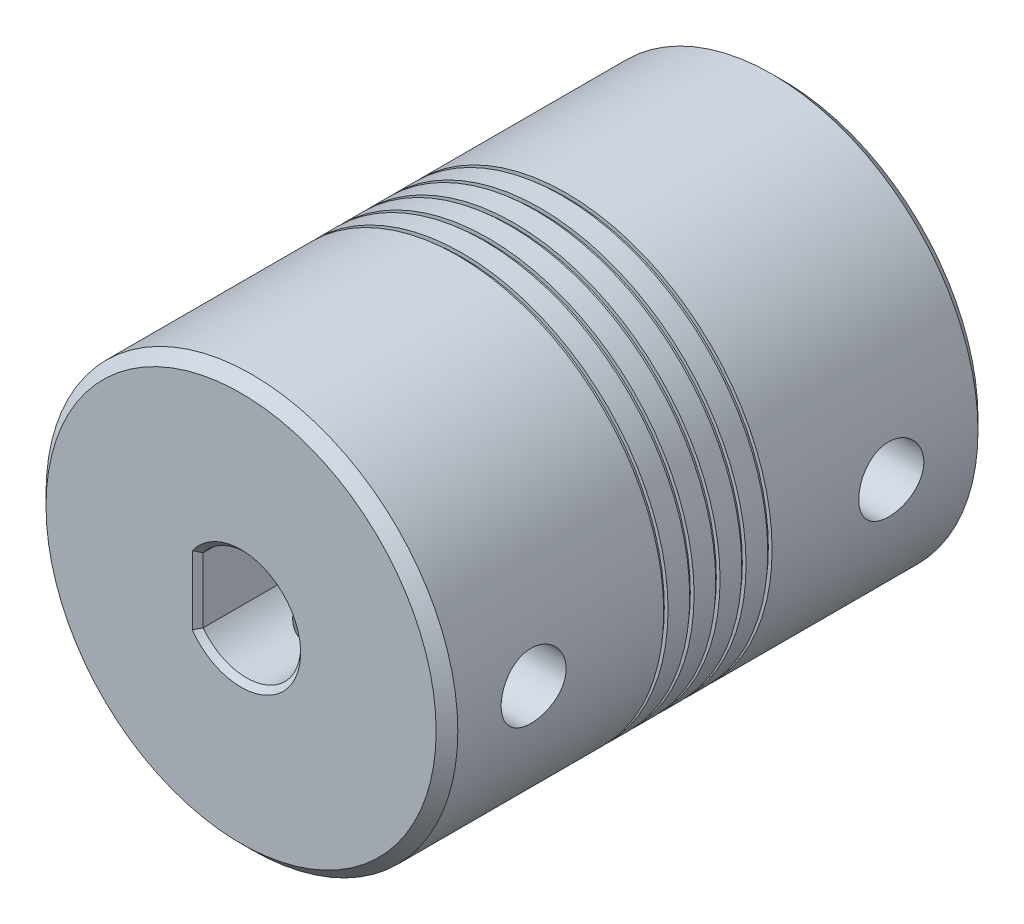
SolidWorks part; units mm, degrees
ref_plane "Ön Düzlem" through (0, 0, 0) normal (0, 0, 1) x (1, 0, 0)
ref_plane "Üst Düzlem" through (0, 0, 0) normal (0, 1, 0) x (1, 0, 0)
ref_plane "Sağ Düzlem" through (0, 0, 0) normal (1, 0, 0) x (0, 0, -1)
sketch "Çizim1" plane through (0, 0, 0) normal (0, 0, 1) x (1, 0, 0)
  circle A0 centre (0, 0) radius 9.5
  dimension "D1" = 19
extrude "Yükseklik-Ekstrüzyon1" add sketch "Çizim1" along normal blind 25
sketch "Çizim2" plane through (0, 0, 25) normal (0, 0, 1) x (1, 0, 0)
  line L0 (-2, -1.5) -> (-2, 1.5)
  arc A0 (-2, -1.5) -> (-2, 1.5) centre (0, 0) ccw
  point P5 (-1.8625, -7.5087)
  point P6 (-1.9038, 4.4887)
  dimension "D1" = 5
extrude "Kes-Ekstrüzyon1" cut sketch "Çizim2" against normal through all
sketch "Çizim3" plane through (0, 0, 0) normal (0, 0, -1) x (-1, 0, 0)
  circle A0 centre (0, 0) radius 4
  dimension "D1" = 8
extrude "Kes-Ekstrüzyon2" cut sketch "Çizim3" against normal blind 10
chamfer "Pah1" distance 0.5 angle 45 2 edges at (9.5, 0, 25) (9.5, 0, 0)
chamfer "Pah2" distance 0.25 angle 45 3 edges at (-4, 0, 0) (-2, 0, 25) (2.5, 0, 25)
sketch "Çizim4" plane through (0, 0, 0) normal (0, 1, 0) x (1, 0, 0)
  line L0 (-9.3279, -10.2) -> (-9.3279, -11.2) construction
  line L1 (-9.792, -10) -> (-9.3279, -10)
  line L2 (-9.792, -10) -> (-9.792, -10.2)
  line L3 (-9.792, -10.2) -> (-9.3279, -10.2)
  line L4 (-9.3279, -10) -> (-9.3279, -10.2)
  line L5 (-9.792, -11.2) -> (-9.3279, -11.2)
  line L6 (-9.792, -11.2) -> (-9.792, -11.4)
  line L7 (-9.792, -11.4) -> (-9.3279, -11.4)
  line L8 (-9.3279, -11.2) -> (-9.3279, -11.4)
  line L9 (-9.792, -12.4) -> (-9.3279, -12.4)
  line L10 (-9.792, -12.4) -> (-9.792, -12.6)
  line L11 (-9.792, -12.6) -> (-9.3279, -12.6)
  line L12 (-9.3279, -12.4) -> (-9.3279, -12.6)
  line L13 (-9.792, -13.6) -> (-9.3279, -13.6)
  line L14 (-9.792, -13.6) -> (-9.792, -13.8)
  line L15 (-9.792, -13.8) -> (-9.3279, -13.8)
  line L16 (-9.3279, -13.6) -> (-9.3279, -13.8)
  line L17 (-9.792, -14.8) -> (-9.3279, -14.8)
  line L18 (-9.792, -14.8) -> (-9.792, -15)
  line L19 (-9.792, -15) -> (-9.3279, -15)
  line L20 (-9.3279, -14.8) -> (-9.3279, -15)
  line L21 (-9.3279, -11.4) -> (-9.3279, -12.4) construction
  line L22 (-9.3279, -12.6) -> (-9.3279, -13.6) construction
  line L23 (-9.3279, -13.8) -> (-9.3279, -14.8) construction
  line L24 (-9.5, -0.5) -> (-9.5, -24.5) construction
  line L25 (0, 4.8733) -> (0, -30.3265) construction
  point P22 (-9.5, -12.5)
  point P25 (-9.3279, -12.5)
  dimension "D1" = 0.2
  dimension "D2" = 1
revolve "Kes-Döndür1" cut sketch "Çizim4" angle 360 about L25
ref_plane "Düzlem1" through (0, -9.5, 0) normal (0, -1, 0) x (-1, 0, 0)
sketch "Çizim5" plane through (0, -9.5, 0) normal (0, -1, 0) x (-1, 0, 0)
  line L0 (-9.5, -24.5) -> (9.5, -24.5) construction
  line L1 (9, 0) -> (-9, 0) construction
  circle A0 centre (0, -20.5) radius 1.5
  circle A1 centre (0, -4) radius 1.5
  dimension "D1" = 3
  dimension "D2" = 4
  dimension "D3" = 4
extrude "Kes-Ekstrüzyon3" cut sketch "Çizim5" against normal up to next
ref_plane "Düzlem2" through (9.5, 0, 0) normal (1, 0, 0) x (0, 0, -1)
sketch "Çizim6" plane through (9.5, 0, 0) normal (1, 0, 0) x (0, 0, -1)
  line L0 (-0.5, 9.5) -> (-0.5, -9.5) construction
  line L1 (-25, 9) -> (-25, -9) construction
  circle A0 centre (-21, 0) radius 1.5
  circle A1 centre (-4.5, 0) radius 1.5
  point P6 (0, 0)
  dimension "D1" = 3
  dimension "D2" = 3
  dimension "D3" = 4
  dimension "D4" = 4
extrude "Kes-Ekstrüzyon4" cut sketch "Çizim6" against normal up to next
